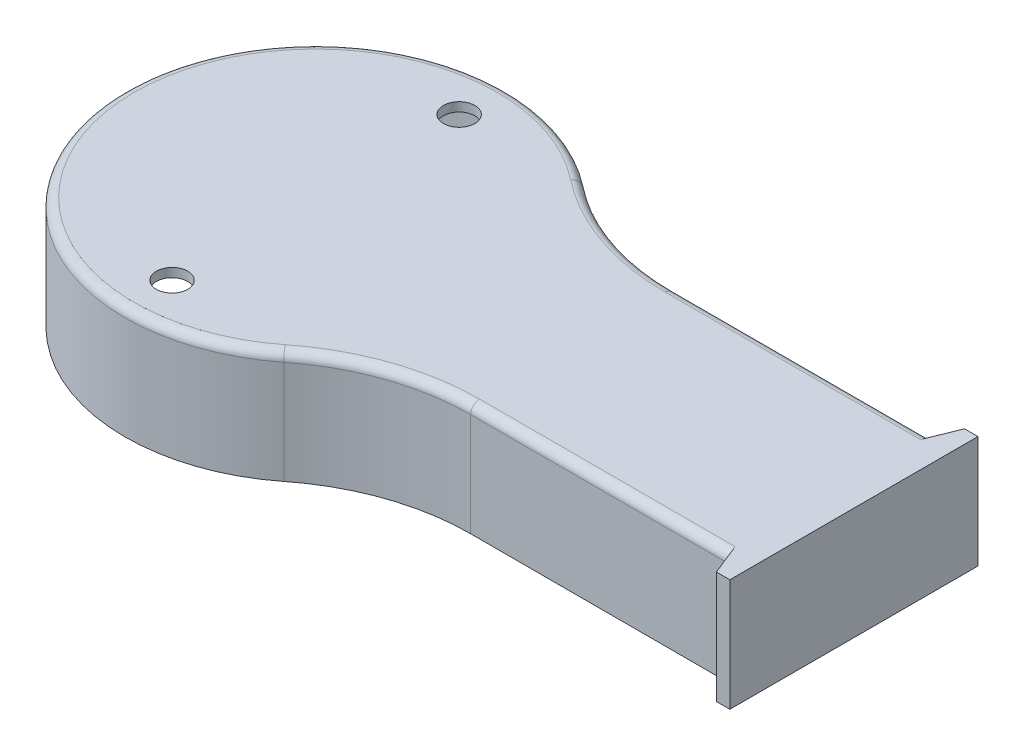
SolidWorks part; units mm, degrees
ref_plane "Alzado" through (0, 0, 0) normal (0, 0, 1) x (1, 0, 0)
ref_plane "Planta" through (0, 0, 0) normal (0, 1, 0) x (1, 0, 0)
ref_plane "Vista lateral" through (0, 0, 0) normal (1, 0, 0) x (0, 0, -1)
sketch "Croquis1" plane through (0, 0, 0) normal (0, 1, 0) x (1, 0, 0)
  line L1 (57.2403, 0) -> (120, 0)
  line L3 (57.2403, 45.3245) -> (120, 45.3245)
  line L4 (120, 0) -> (120, 45.3245)
  arc A0 (26.2996, 56.0476) -> (26.2996, -10.7231) centre (0, 22.6622) ccw
  arc A1 (57.2403, 45.3245) -> (26.2996, 56.0476) centre (57.2403, 95.3245) cw
  arc A2 (57.2403, 0) -> (26.2996, -10.7231) centre (57.2403, -50) ccw
  dimension "D1" = 85
  dimension "D3" = 50
  dimension "D2" = 120
extrude "Saliente-Extruir1" add sketch "Croquis1" along normal blind 25
shell "Vaciado1" thickness 2
sketch "Croquis3" plane through (0, 25, 0) normal (0, 1, 0) x (1, 0, 0)
  circle A0 centre (0, 22.6622) radius 32 construction
  circle A1 centre (0, 54.6622) radius 3.5
  circle A2 centre (0, -9.3378) radius 3.5
  dimension "D1" = 64
  dimension "D2" = 7
extrude "Cortar-Extruir1" cut sketch "Croquis3" against normal up to next
sketch "Croquis4" plane through (0, 25, 0) normal (0, 1, 0) x (1, 0, 0)
  line L0 (120, 45.3245) -> (120, 50.3245)
  line L1 (120, 50.3245) -> (117, 50.3245)
  line L2 (117, 50.3245) -> (115, 45.3245)
  line L3 (120, 45.3245) -> (57.2403, 45.3245) construction
  line L4 (115, 45.3245) -> (120, 45.3245)
  line L5 (120, 22.6622) -> (101.7294, 22.6622) construction
  line L6 (120, 0) -> (120, 45.3245) construction
  line L7 (115, 0) -> (120, 0)
  line L8 (117, -5) -> (115, 0)
  line L9 (120, -5) -> (117, -5)
  line L10 (120, 0) -> (120, -5)
  dimension "D1" = 5
  dimension "D2" = 5
  dimension "D3" = 3
extrude "Saliente-Extruir2" add sketch "Croquis4" against normal up to surface (25 mm away) up to face at (55.5275, 0, -22.6622)
fillet "Redondeo1" radius 2 5 edges at (86.1201, 25, -45.3245) (40.8672, 25, -48.0812) (-42.5, 25, -22.6622) (40.8672, 25, 2.7568) (86.1201, 25, 0)
fillet "Redondeo2" radius 2 6 edges at (-40.5, 23, -22.6622) (40.2123, 23, 0.867) (87.6201, 23, -2) (118, 23, -22.6622) (87.6201, 23, -43.3245) (40.2123, 23, -46.1915)
